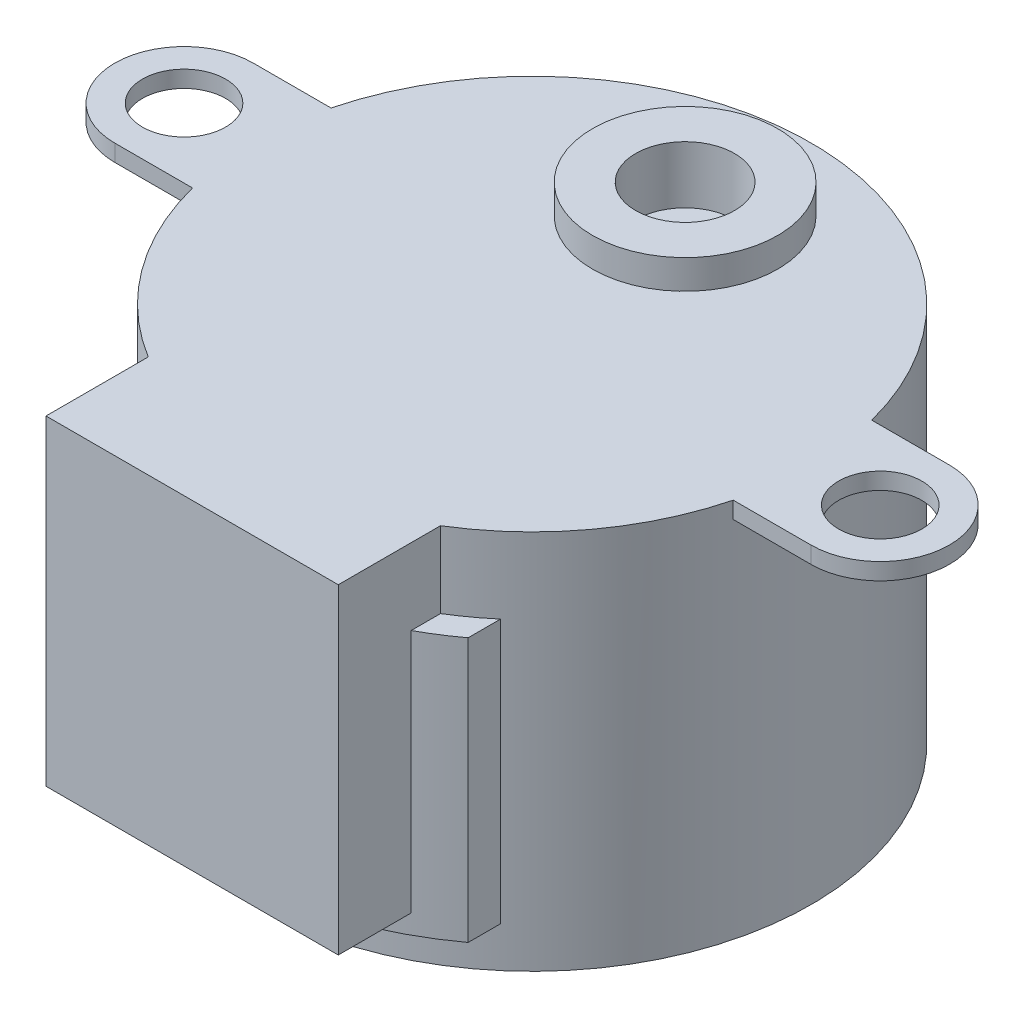
SolidWorks part; units mm, degrees
ref_plane "Front Plane" through (0, 0, 0) normal (0, 0, 1) x (1, 0, 0)
ref_plane "Top Plane" through (0, 0, 0) normal (0, 1, 0) x (1, 0, 0)
ref_plane "Right Plane" through (0, 0, 0) normal (1, 0, 0) x (0, 0, -1)
sketch "Sketch1" plane through (0, 0, 0) normal (0, 1, 0) x (1, 0, 0)
  circle A0 centre (0, 0) radius 13.97
  dimension "D1" = 27.94
extrude "Boss-Extrude1" add sketch "Sketch1" along normal blind 19.05
sketch "Sketch2" plane through (0, 19.05, 0) normal (0, 1, 0) x (1, 0, 0)
  line L0 (0, 13.97) -> (0, 3.0226) construction
  circle A0 centre (0, 7.6581) radius 4.6355
  circle A1 centre (0, 0) radius 13.97 construction
  dimension "D1" = 9.271
  dimension "D2" = 10.9474
extrude "Boss-Extrude2" add sketch "Sketch2" along normal blind 1.4605
sketch "Sketch3" plane through (0, 20.5105, 0) normal (0, 1, 0) x (1, 0, 0)
  circle A0 centre (0, 7.6581) radius 2.4765
  dimension "D1" = 4.953
extrude "Boss-Extrude3" add sketch "Sketch3" along normal blind 7.8232
sketch "Sketch5" plane through (0, 28.3337, 0) normal (0, 1, 0) x (1, 0, 0)
  line L0 (-2, 9.1186) -> (2, 9.1186)
  line L1 (0, 9.1186) -> (0, 6.1976) construction
  line L2 (2, 6.1976) -> (-2, 6.1976)
  circle A1 centre (0, 7.6581) radius 2.4765
  circle A2 centre (0, 7.6581) radius 2.4765
  point P9 (0, 7.6581)
  circle M4 centre (0, 7.6581) radius 2.4765
  dimension "D2" = 2.921
  dimension "D1" = 0
extrude "Cut-Extrude1" cut sketch "Sketch5" against normal blind 6.2611 contours L0 M4 | L2 M4
sketch "Sketch6" plane through (0, 19.05, 0) normal (0, 1, 0) x (1, 0, 0)
  line L0 (-17.4244, 3.4671) -> (-13.5329, 3.4671)
  line L1 (17.4244, 3.4671) -> (13.5329, 3.4671)
  line L2 (17.4244, -3.4671) -> (13.5329, -3.4671)
  line L3 (-17.4244, -3.4671) -> (-13.5329, -3.4671)
  line L4 (-20.8915, 0) -> (20.8915, 0) construction
  circle A0 centre (0, 0) radius 13.97 construction
  arc A1 (17.4244, -3.4671) -> (17.4244, 3.4671) centre (17.4244, 0) ccw
  circle A2 centre (17.4244, 0) radius 2.0828
  arc A3 (-17.4244, 3.4671) -> (-17.4244, -3.4671) centre (-17.4244, 0) ccw
  circle A4 centre (0, 0) radius 13.97
  arc A5 (-13.5329, 3.4671) -> (-13.5329, -3.4671) centre (0, 0) ccw
  circle A6 centre (-17.4244, 0) radius 2.0828
  arc A7 (13.5329, -3.4671) -> (13.5329, 3.4671) centre (0, 0) ccw
  point P1 (-13.97, 0)
  point P22 (0, 0)
  circle M13 centre (0, 0) radius 13.97
  dimension "D1" = 6.9342
  dimension "D2" = 4.1656
  dimension "D4" = 41.783
  dimension "D5" = 3.4544
  dimension "D3" = 0
extrude "Boss-Extrude4" add sketch "Sketch6" against normal blind 0.8382 contours A3 L4 A6 A5 L0 M13 | L4 A3 L3 A6 M13 | L4 A2 A1 L1 M13 | L4 A7 L2 A1 A2 M13
sketch "Sketch7" plane through (0, 19.05, 0) normal (0, 1, 0) x (1, 0, 0)
  line L0 (0, 13.97) -> (0, -17.018) construction
  line L3 (7.3152, -17.018) -> (-7.3152, -17.018)
  line L4 (-7.3152, -11.9016) -> (-7.3152, -17.018)
  line L5 (7.3152, -6.3252) -> (-7.3152, -17.018) construction
  line L6 (7.3152, -17.018) -> (0, -11.6716) construction
  line L7 (7.3152, -11.9016) -> (7.3152, -17.018)
  line L8 (7.3152, -6.3252) -> (7.3152, -11.9016) construction
  arc A0 (-13.5329, -3.4671) -> (13.5329, -3.4671) centre (0, 0) ccw construction
  arc A1 (-7.3152, -11.9016) -> (7.3152, -11.9016) centre (0, 0) ccw
  arc A2 (13.5329, 3.4671) -> (-13.5329, 3.4671) centre (0, 0) ccw construction
  point P0 (0, -11.6716)
  dimension "D1" = 14.6304
  dimension "D2" = 30.988
  dimension "D3" = 10.6928
extrude "Boss-Extrude5" add sketch "Sketch7" against normal blind 16.0528
ref_plane "Plane1" through (0, 15.24, 0) normal (0, 1, 0) x (1, 0, 0)
sketch "Sketch8" plane through (0, 15.24, 0) normal (0, 1, 0) x (1, 0, 0)
  line L1 (0, 13.97) -> (0, -15.24) construction
  line L2 (-9.0551, -10.638) -> (-9.0551, -12.2582)
  line L3 (9.0551, -10.638) -> (9.0551, -12.2582)
  arc A0 (9.0551, -12.2582) -> (-9.0551, -12.2582) centre (0, 0) cw
  arc A1 (13.5329, 3.4671) -> (-13.5329, 3.4671) centre (0, 0) ccw construction
  arc A2 (14.7632, -3.7823) -> (-14.7632, -3.7823) centre (0, 0) cw construction
  arc A3 (13.5329, -3.4671) -> (-13.5329, -3.4671) centre (0, 0) cw construction
  arc A4 (-13.5329, -3.4671) -> (-7.3152, -11.9016) centre (0, 0) ccw construction
  arc A6 (9.0551, -10.638) -> (-9.0551, -10.638) centre (0, 0) cw
  dimension "D1" = 29.21
  dimension "D2" = 18.1102
extrude "Boss-Extrude6" add sketch "Sketch8" against normal blind 13.208
sketch "Sketch9" plane through (0, 28.3337, 0) normal (0, 1, 0) x (1, 0, 0)
  circle A0 centre (0, 7.6581) radius 2.4765 construction
  circle A1 centre (0, 7.6581) radius 2.4765
extrude "Cut-Extrude2" cut sketch "Sketch9" against normal blind 10.6934
